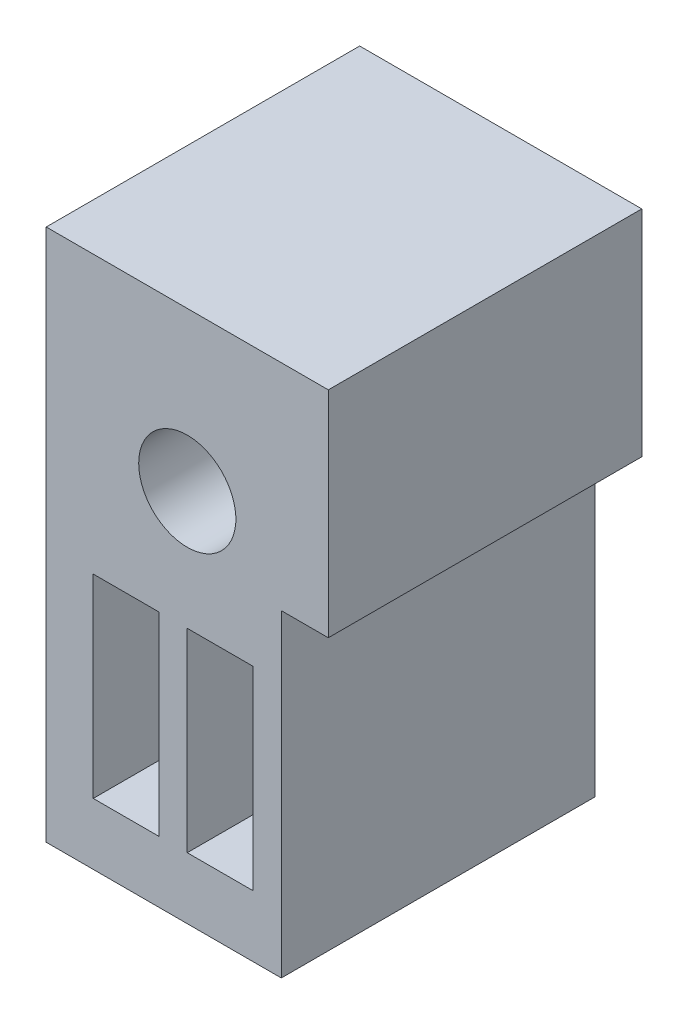
SolidWorks part; units mm, degrees
ref_plane "Ebene vorne" through (0, 0, 0) normal (0, 0, 1) x (1, 0, 0)
ref_plane "Ebene oben" through (0, 0, 0) normal (0, 1, 0) x (1, 0, 0)
ref_plane "Ebene rechts" through (0, 0, 0) normal (1, 0, 0) x (0, 0, -1)
sketch "Skizze2" plane through (0, 0, -20.1695) normal (0, 0, -1) x (-1, 0, 0)
  line L0 (-19.1481, 32.227) -> (-19.1481, 15.227) construction
  line L1 (-22.1481, 15.227) -> (-19.1481, 15.227)
  line L2 (-19.1481, 32.227) -> (-23.6481, 32.227)
  line L3 (-19.1481, 15.227) -> (-16.4481, 15.227)
  line L4 (-14.6481, 32.227) -> (-14.6481, 25.3772)
  line L5 (-19.1481, 32.227) -> (-14.6481, 32.227)
  line L6 (-23.6481, 32.227) -> (-23.6481, 25.3772)
  line L7 (-23.6481, 23.727) -> (-14.6481, 23.727) construction
  line L8 (-19.1481, 27.1767) -> (-16.2491, 27.1767) construction
  line L9 (-19.1481, 20.2772) -> (-16.2491, 20.2772) construction
  line L10 (-19.4975, 17.1882) -> (-16.1481, 17.1882) construction
  line L11 (-19.4975, 23.3882) -> (-16.1481, 23.3882) construction
  line L12 (-19.7481, 32.227) -> (-19.7481, 15.227) construction
  line L13 (-18.5481, 32.227) -> (-18.5481, 15.227) construction
  line L14 (-21.8481, 32.227) -> (-21.8481, 15.227) construction
  line L15 (-16.4481, 32.227) -> (-16.4481, 15.227) construction
  line L16 (-16.1481, 23.3882) -> (-18.2481, 23.3882)
  line L17 (-14.6481, 25.3772) -> (-14.6481, 15.227)
  line L18 (-18.2481, 17.1882) -> (-16.1481, 17.1882)
  line L19 (-18.2481, 23.3882) -> (-18.2481, 17.1882)
  line L20 (-19.147, 17.1882) -> (-19.147, 23.3882)
  line L21 (-21.247, 17.1882) -> (-19.147, 17.1882)
  line L22 (-21.247, 23.3882) -> (-21.247, 17.1882)
  line L23 (-19.147, 23.3882) -> (-21.247, 23.3882)
  line L24 (-14.6481, 15.227) -> (-16.1481, 15.227)
  line L25 (-14.6481, 23.3882) -> (-16.1481, 23.3882) construction
  line L27 (-16.1481, 15.227) -> (-16.4481, 15.227)
  line L28 (-23.6481, 25.3772) -> (-22.1481, 25.3772)
  line L29 (-22.1481, 25.3772) -> (-22.1481, 15.227)
  line L30 (-16.1481, 23.3882) -> (-16.1481, 17.1882)
  circle A0 centre (-19.1481, 27.1767) radius 1.55
extrude "Aufsatz-Linear austragen1" add sketch "Skizze2" along normal blind 10
